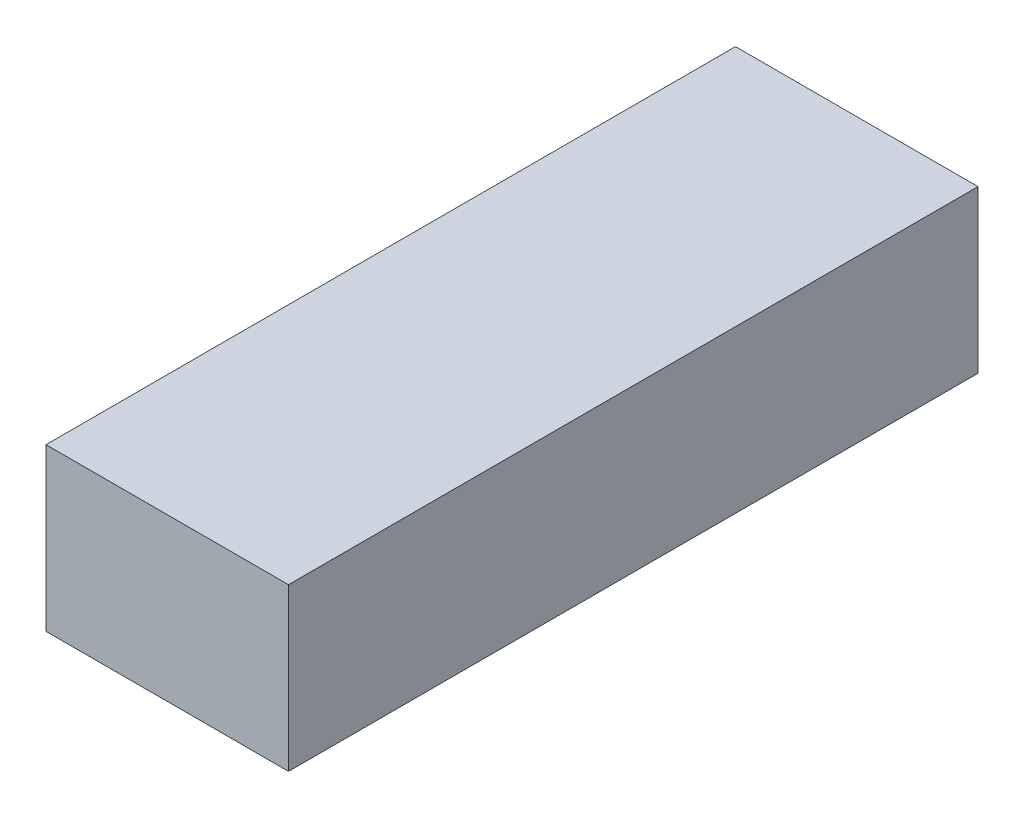
SolidWorks part; units mm, degrees
ref_plane "Front Plane" through (0, 0, 0) normal (0, 0, 1) x (1, 0, 0)
ref_plane "Top Plane" through (0, 0, 0) normal (0, 1, 0) x (1, 0, 0)
ref_plane "Right Plane" through (0, 0, 0) normal (1, 0, 0) x (0, 0, -1)
sketch "Sketch1" plane through (0, 0, 0) normal (0, 0, 1) x (1, 0, 0)
  line L1 (-25.5, -17) -> (25.5, -17)
  line L2 (-25.5, -17) -> (-25.5, 17)
  line L3 (-25.5, 17) -> (25.5, 17)
  line L4 (25.5, -17) -> (25.5, 17)
  line L5 (-25.5, -17) -> (25.5, 17) construction
  line L6 (-25.5, 17) -> (25.5, -17) construction
  point P0 (0, 0)
  dimension "D1" = 51
  dimension "D2" = 34
extrude "Boss-Extrude1" add sketch "Sketch1" along normal blind 145
